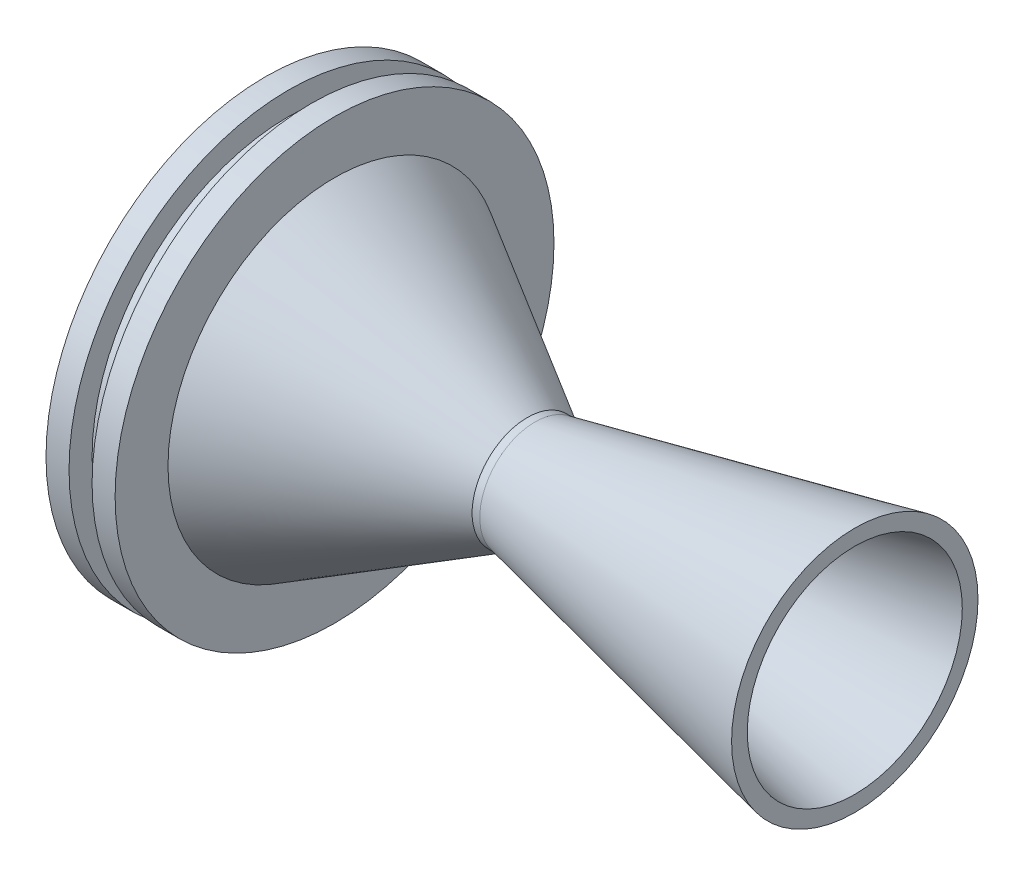
SolidWorks part; units mm, degrees
material "AISI 1020"
ref_plane "Plano frontal" through (0, 0, 0) normal (0, 0, 1) x (1, 0, 0)
ref_plane "Plano superior" through (0, 0, 0) normal (0, 1, 0) x (1, 0, 0)
ref_plane "Plano direito" through (0, 0, 0) normal (1, 0, 0) x (0, 0, -1)
sketch "Esboço1" plane through (0, 0, 0) normal (0, 0, 1) x (1, 0, 0)
  line L0 (0, 0) -> (-50000, 0) construction
  line L1 (0, -1000) -> (0, 49000) construction
  line L2 (0, 28.575) -> (0, 24.575)
  line L3 (0, 24.575) -> (33.9049, 5)
  line L4 (33.9049, 5) -> (34.4049, 5)
  line L5 (34.4049, 5) -> (76.7466, 14)
  line L6 (76.7466, 14) -> (76.7466, 16.0447)
  line L7 (76.7466, 16.0447) -> (35.1055, 7.1936)
  line L8 (35.1055, 7.1936) -> (34.1055, 7.1936)
  line L9 (34.1055, 7.1936) -> (9, 21.6882)
  line L10 (9, 21.6882) -> (9, 28.575)
  line L11 (9, 28.575) -> (6, 28.575)
  line L12 (3, 28.575) -> (0, 28.575)
  line L14 (3, 28.575) -> (3, 25.575)
  line L15 (3, 25.575) -> (6, 25.575)
  line L16 (6, 28.575) -> (6, 25.575)
  dimension "D1" = 28.575
  dimension "D2" = 3
  dimension "D3" = 3
  dimension "D4" = 3
  dimension "D5" = 3
  dimension "D6" = 1
  dimension "D7" = 0.5
  dimension "D9" = 30
  dimension "D10" = 12
  dimension "D11" = 4
  dimension "D12" = 5
  dimension "D13" = 14
  dimension "D14" = 2
  dimension "D8" = 2
revolve "Revolução1" add sketch "Esboço1" angle 360 about L0
equation "\"D1@Esboço1\"=25.4*(2.5-2*(1/8))/2"
equation "\"D8@Esboço1\"=\"D14@Esboço1\""
